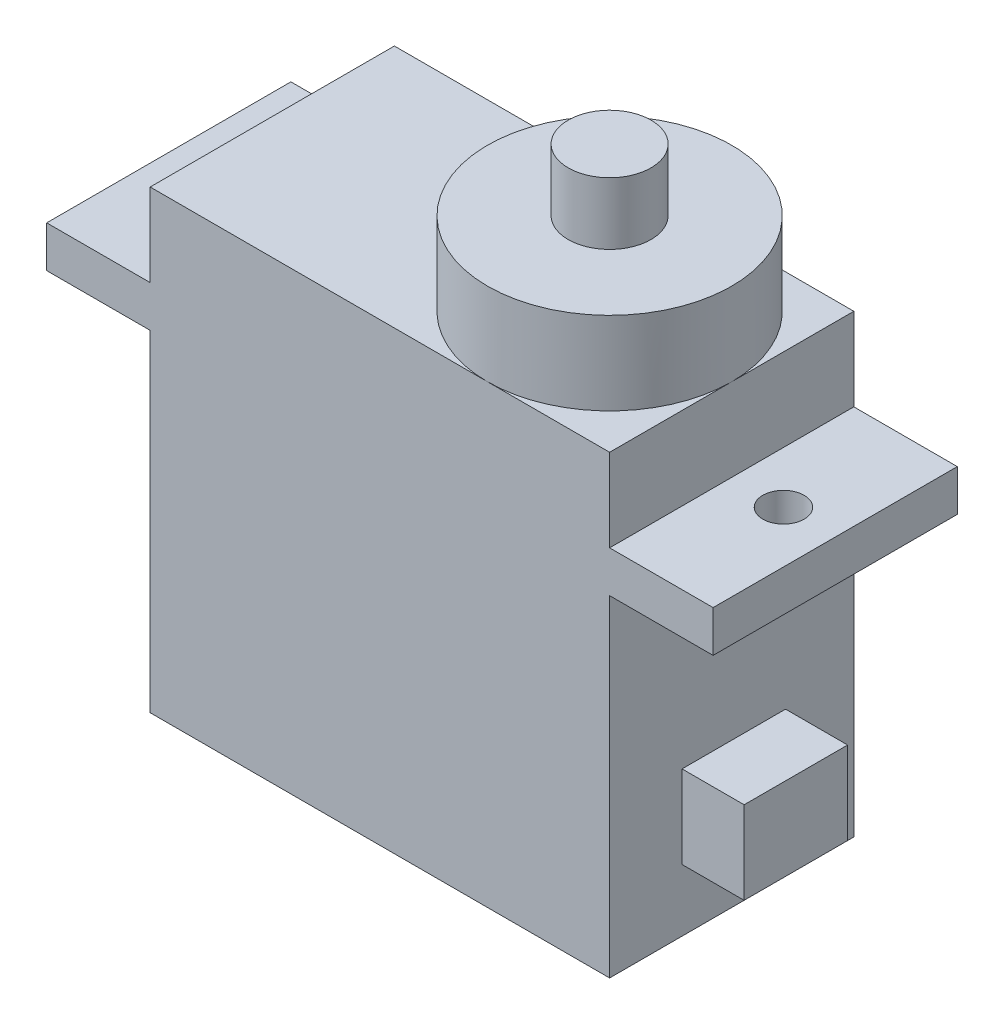
SolidWorks part; units mm, degrees
ref_plane "Plan de face" through (0, 0, 0) normal (0, 0, 1) x (1, 0, 0)
ref_plane "Plan de dessus" through (0, 0, 0) normal (0, 1, 0) x (1, 0, 0)
ref_plane "Plan de droite" through (0, 0, 0) normal (1, 0, 0) x (0, 0, -1)
sketch "Esquisse1" plane through (0, 0, 0) normal (0, 0, 1) x (1, 0, 0)
  line L0 (-45.1965, 18) -> (-40.1965, 18)
  line L1 (-40.1965, 18) -> (-40.1965, 22)
  line L2 (-40.1965, 22) -> (-17.9965, 22)
  line L3 (-17.9965, 22) -> (-17.9965, 18)
  line L4 (-17.9965, 18) -> (-12.9965, 18)
  line L5 (-12.9965, 18) -> (-12.9965, 16)
  line L6 (-12.9965, 16) -> (-17.9965, 16)
  line L7 (-17.9965, 16) -> (-17.9965, 0)
  line L8 (-17.9965, 0) -> (-40.1965, 0)
  line L9 (-40.1965, 0) -> (-40.1965, 16)
  line L10 (-40.1965, 16) -> (-45.1965, 16)
  line L11 (-45.1965, 16) -> (-45.1965, 18)
  dimension "D1" = 22.2
  dimension "D2" = 22.2
  dimension "D3" = 32.2
  dimension "D4" = 5
  dimension "D5" = 16
  dimension "D6" = 2
  dimension "D7" = 16
  dimension "D8" = 2
  dimension "D9" = 4
extrude "Boss.-Extru.1" add sketch "Esquisse1" along normal blind 11.8
sketch "Esquisse2" plane through (0, 18, 0) normal (0, 1, 0) x (1, 0, 0)
  line L0 (-40.1965, -11.8) -> (-40.1965, 0) construction
  line L1 (-17.9965, 0) -> (-40.1965, 0) construction
  line L2 (-12.9965, 0) -> (-17.9965, 0) construction
  line L3 (-17.9965, -11.8) -> (-17.9965, 0) construction
  circle A0 centre (-42.6965, -5.9) radius 1
  circle A1 centre (-15.4965, -5.9) radius 1
  dimension "D1" = 2.5
  dimension "D2" = 2
  dimension "D3" = 5.9
  dimension "D4" = 5.9
  dimension "D5" = 2.5
  dimension "D6" = 2
extrude "Enlèv. mat.-Extru.1" cut sketch "Esquisse2" against normal blind 11.8
sketch "Esquisse3" plane through (0, 22, 0) normal (0, 1, 0) x (1, 0, 0)
  line L0 (-17.9965, 0) -> (-40.1965, 0) construction
  line L1 (-17.9965, -11.8) -> (-17.9965, 0) construction
  circle A0 centre (-23.8965, -5.9) radius 5.9
  dimension "D1" = 11.8
  dimension "D2" = 5.9
  dimension "D3" = 5.9
extrude "Boss.-Extru.2" add sketch "Esquisse3" along normal blind 4
sketch "Esquisse4" plane through (0, 26, 0) normal (0, 1, 0) x (1, 0, 0)
  line L0 (-23.8965, 0) -> (-40.1965, 0) construction
  line L1 (-17.9965, -11.8) -> (-17.9965, 0) construction
  circle A0 centre (-23.8965, -5.9) radius 2
  dimension "D1" = 4
  dimension "D2" = 5.9
  dimension "D3" = 5.9
extrude "Boss.-Extru.3" add sketch "Esquisse4" along normal blind 3
sketch "Esquisse5" plane through (-17.9965, 0, 0) normal (1, 0, 0) x (0, 0, -1)
  line L0 (-11.8, 0) -> (-11.8, 16) construction
  line L1 (-8.3, 3) -> (-3.3, 3)
  line L2 (-8.3, 3) -> (-8.3, 7)
  line L3 (-8.3, 7) -> (-3.3, 7)
  line L4 (-3.3, 3) -> (-3.3, 7)
  line L5 (-11.8, 0) -> (0, 0) construction
  dimension "D1" = 5
  dimension "D2" = 3.5
  dimension "D3" = 4
  dimension "D4" = 3
extrude "Boss.-Extru.4" add sketch "Esquisse5" along normal blind 3
